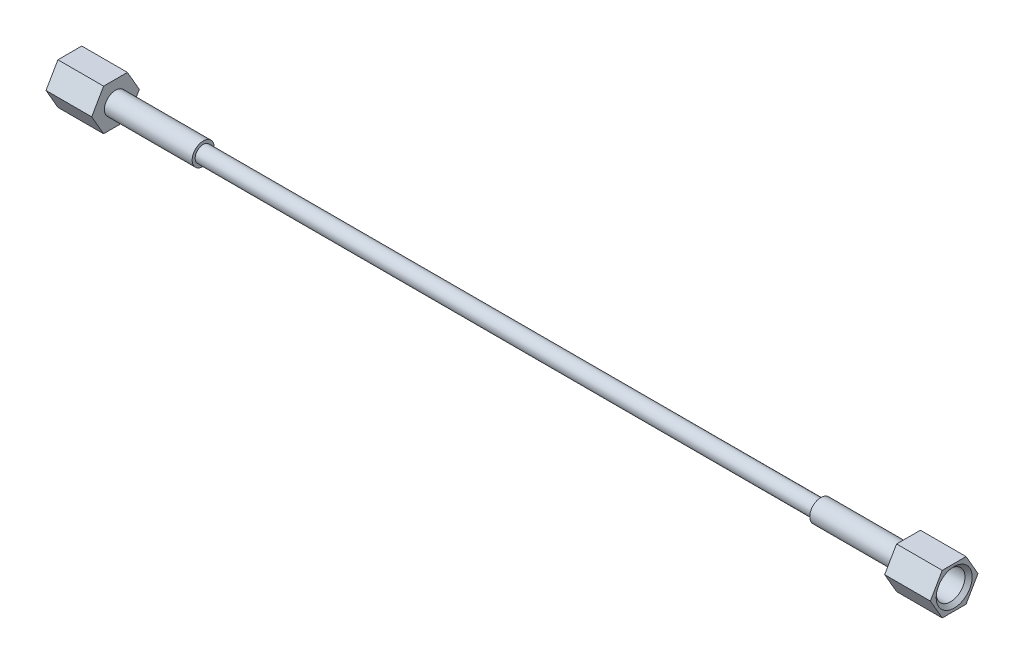
SolidWorks part; units mm, degrees
material "Alloy Steel"
ref_plane "Front Plane" through (0, 0, 0) normal (0, 0, 1) x (1, 0, 0)
ref_plane "Top Plane" through (0, 0, 0) normal (0, 1, 0) x (1, 0, 0)
ref_plane "Right Plane" through (0, 0, 0) normal (1, 0, 0) x (0, 0, -1)
ref_plane "Plane5" through (-6.858, 0, 0) normal (1, 0, 0) x (0, 0, -1)
sketch "Sketch5" plane through (-6.858, 0, 0) normal (1, 0, 0) x (0, 0, -1)
  line L0 (4.1061, 7.112) -> (-4.1061, 7.112)
  line L1 (-4.1061, 7.112) -> (-8.2122, 0)
  line L2 (-8.2122, 0) -> (-4.1061, -7.112)
  line L3 (-4.1061, -7.112) -> (4.1061, -7.112)
  line L4 (4.1061, -7.112) -> (8.2122, 0)
  line L5 (8.2122, 0) -> (4.1061, 7.112)
extrude "Extrude2" add sketch "Sketch5" along normal blind 15.748 separate body
hole_wizard "Hole2" positions "Sketch7" profile "Sketch6" legacy end condition up to next
sketch "Sketch7" plane through (8.89, 0, 0) normal (1, 0, 0) x (0, 0, -1)
  point P0 (0, 0)
sketch "Sketch6" plane through (8.89, 0, 0) normal (0, 1, 0) x (0, 0, -1)
  line L0 (0, 0) -> (0, 15.748)
  line L1 (0, 15.748) -> (3.8354, 15.748)
  line L2 (3.8354, 15.748) -> (3.8354, 9.5661)
  line L3 (3.8354, 9.5661) -> (4.9606, 8.89)
  line L4 (4.9606, 8.89) -> (4.9606, 0)
  line L5 (4.9606, 0) -> (0, 0)
  line L6 (0, -6.13) -> (0, 109.2824) construction
  line L7 (-3.8354, 9.5661) -> (-4.9606, 8.89) construction
  line L8 (0, 15.748) -> (-3.8354, 15.748) construction
  dimension "Diameter" = 7.6708
  dimension "Depth" = 15.748
  dimension "C-Drill Diameter" = 9.9212
  dimension "C-Drill Depth" = 8.89
  dimension "C-Drill Angle" = 118
chamfer "Chamfer2" distance 1.2402 angle 45 1 edges at (8.89, 0, -4.9606)
ref_plane "Plane4" through (0, 0, 0) normal (0, 0, -1) x (-1, 0, 0)
sketch "Sketch8" plane through (0, 0, 0) normal (0, 0, -1) x (-1, 0, 0)
  line L0 (0.6914, 3.81) -> (2.3854, 0.9906)
  line L1 (2.3854, 0.9906) -> (284.6346, 0.9906)
  line L2 (249.936, 3.81) -> (286.3286, 3.81)
  line L3 (249.936, 2.7686) -> (249.936, 3.81)
  line L4 (286.3286, 3.81) -> (284.6346, 0.9906)
  line L5 (249.936, 2.7686) -> (37.084, 2.7686)
  line L6 (37.084, 2.7686) -> (37.084, 3.81)
  line L7 (37.084, 3.81) -> (0.6914, 3.81)
  line L8 (0.6914, 0) -> (202.5086, 0) construction
  line L9 (143.51, 24.5048) -> (143.51, -25.5618) construction
  line L10 (6.858, 7.112) -> (6.858, 0) construction
  line L13 (0.6761, 3.8354) -> (0, 4.9606) construction
  dimension "D1" = 152.4
  dimension "D2" = 1.9812
  dimension "D3" = 5.5372
  dimension "D4" = 7.62
  dimension "D6" = 30.226
revolve "Revolve2" add sketch "Sketch8" angle 360 about L8
ref_plane "Plane6" through (-143.51, 0, 0) normal (1, 0, 0) x (0, 0, -1)
mirror "Mirror2" about plane through (-143.51, 0, 0) normal (1, 0, 0) of bodies 118
